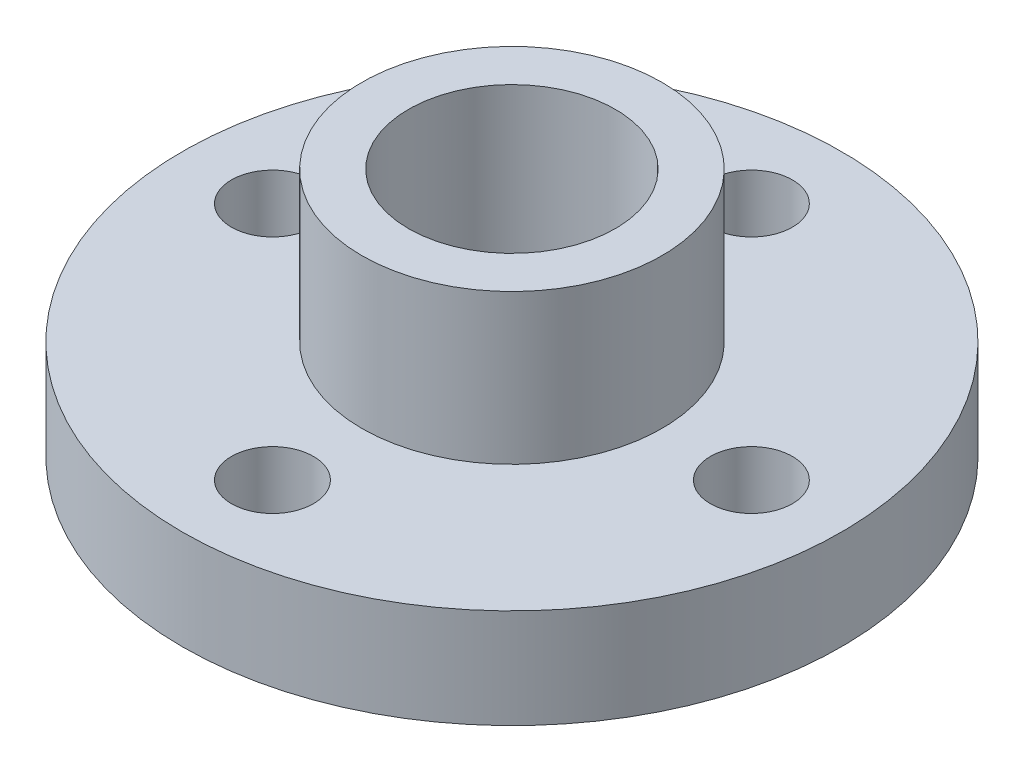
SolidWorks part; units mm, degrees
ref_plane "Front Plane" through (0, 0, 0) normal (0, 0, 1) x (1, 0, 0)
ref_plane "Top Plane" through (0, 0, 0) normal (0, 1, 0) x (1, 0, 0)
ref_plane "Right Plane" through (0, 0, 0) normal (1, 0, 0) x (0, 0, -1)
sketch "Sketch1" plane through (0, 0, 0) normal (0, 1, 0) x (1, 0, 0)
  circle A0 centre (0, 0) radius 11.01
  dimension "D1" = 22.02
extrude "Boss-Extrude1" add sketch "Sketch1" along normal blind 3.32
sketch "Sketch3" plane through (0, 3.32, 0) normal (0, 1, 0) x (1, 0, 0)
  line L0 (0, -11.01) -> (0, 11.01) construction
  line L1 (-11.01, 0) -> (11.01, 0) construction
  circle A0 centre (0, 0) radius 8 construction
  circle A1 centre (0, 0) radius 11.01 construction
  circle A2 centre (-8, 0) radius 1.37
  circle A3 centre (0, 8) radius 1.37
  circle A4 centre (8, 0) radius 1.37
  circle A5 centre (0, -8) radius 1.37
  dimension "D1" = 16
  dimension "D2" = 2.74
extrude "Cut-Extrude1" cut sketch "Sketch3" against normal through all and the other way through all
sketch "Sketch4" plane through (0, 3.32, 0) normal (0, 1, 0) x (1, 0, 0)
  circle A0 centre (0, 0) radius 5.015
  dimension "D1" = 10.03
extrude "Boss-Extrude2" add sketch "Sketch4" along normal blind 5
sketch "Sketch5" plane through (0, 0, 0) normal (0, -1, 0) x (1, 0, 0)
  circle A0 centre (0, 0) radius 5.015
  dimension "D1" = 10.03
extrude "Boss-Extrude3" add sketch "Sketch5" along normal blind 2.03
sketch "Sketch6" plane through (0, 8.32, 0) normal (0, 1, 0) x (1, 0, 0)
  circle A0 centre (0, 0) radius 3.455
  dimension "D1" = 6.91
extrude "Cut-Extrude2" cut sketch "Sketch6" against normal through all
